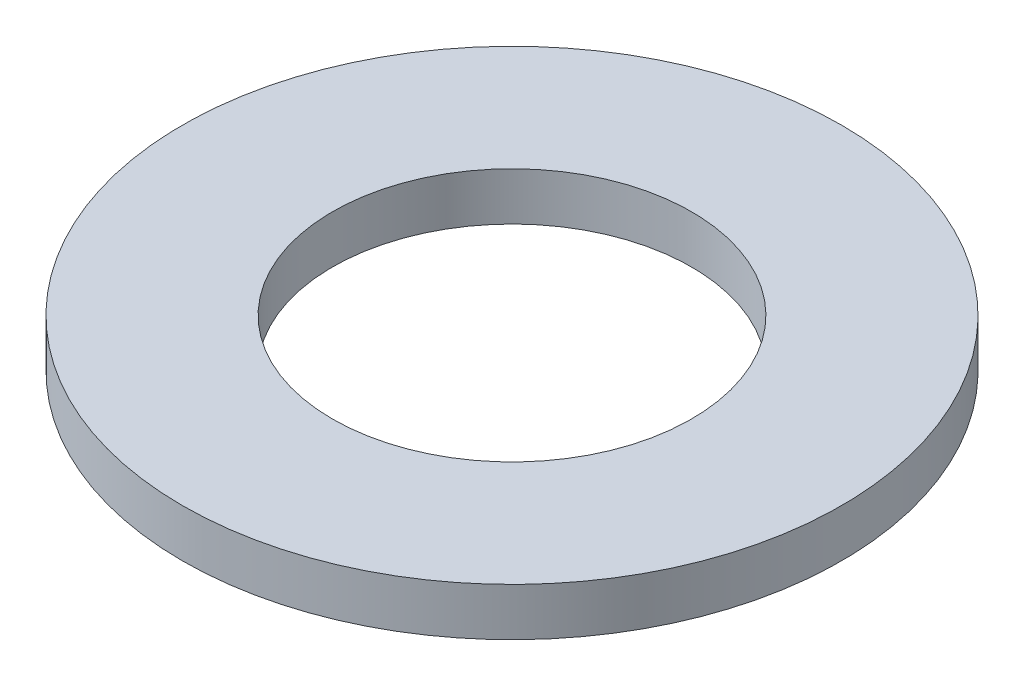
SolidWorks part; units mm, degrees
ref_plane "Front Plane" through (0, 0, 0) normal (0, 0, 1) x (1, 0, 0)
ref_plane "Top Plane" through (0, 0, 0) normal (0, 1, 0) x (1, 0, 0)
ref_plane "Right Plane" through (0, 0, 0) normal (1, 0, 0) x (0, 0, -1)
sketch "Sketch1" plane through (0, 0, 0) normal (0, 1, 0) x (1, 0, 0)
  circle A0 centre (0, 0) radius 5.9436
  dimension "OD" = 11.8872
extrude "Boss-Extrude1" add sketch "Sketch1" along normal blind 0.8636
sketch "Sketch5" plane through (0, 0.8636, 0) normal (0, 1, 0) x (-1, 0, 0)
  circle A0 centre (0, 0) radius 3.2385
  dimension "ID" = 6.477
extrude "Cut-Extrude1" cut sketch "Sketch5" against normal through all
